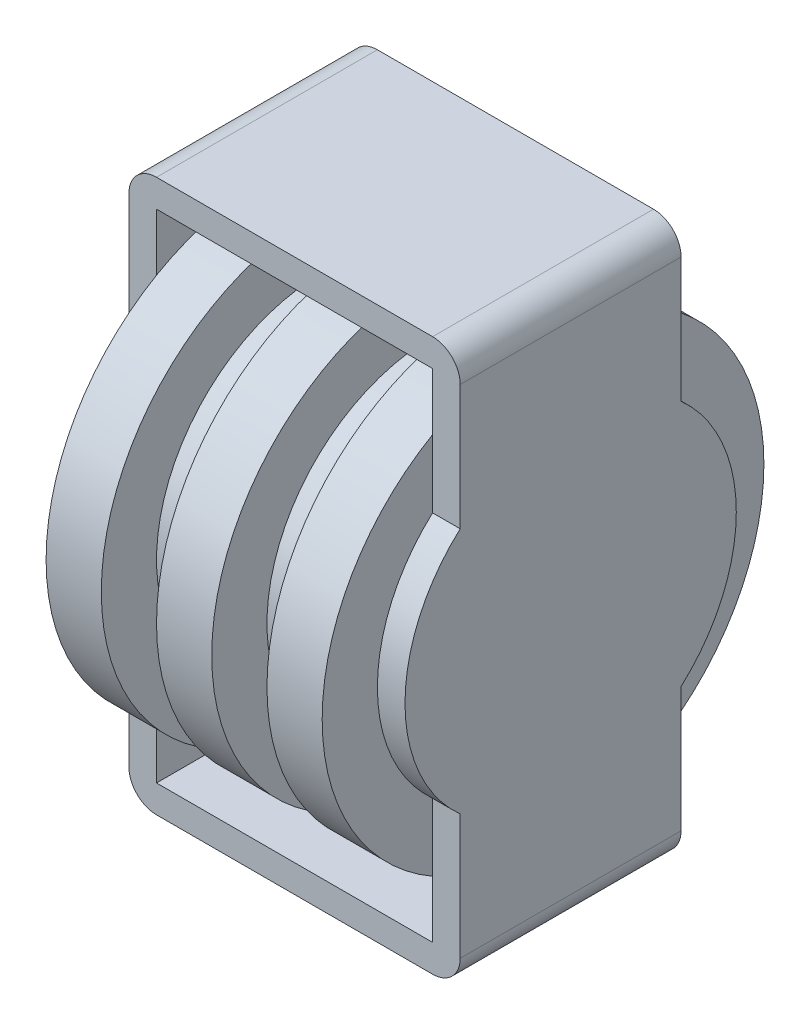
SolidWorks part; units mm, degrees
ref_plane "Front Plane" through (0, 0, 0) normal (0, 0, 1) x (1, 0, 0)
ref_plane "Top Plane" through (0, 0, 0) normal (0, 1, 0) x (1, 0, 0)
ref_plane "Right Plane" through (0, 0, 0) normal (1, 0, 0) x (0, 0, -1)
sketch "Sketch1" plane through (0, 0, 0) normal (1, 0, 0) x (0, 0, -1)
  line L0 (10, -22.5) -> (10, -25)
  line L2 (-10, -22.5) -> (-10, 22.5)
  line L3 (-10, 22.5) -> (10, 22.5)
  line L4 (10, -22.5) -> (10, 22.5)
  line L5 (-10, -22.5) -> (10, 22.5) construction
  line L6 (-10, 22.5) -> (10, -22.5) construction
  line L7 (10, -25) -> (-10, -25)
  line L8 (-10, -25) -> (-10, -22.5)
  circle A2 centre (0, 0) radius 15
  dimension "D1" = 2.5
  dimension "D4" = 30
  dimension "D2" = 20
  dimension "D3" = 45
extrude "Boss-Extrude1" add sketch "Sketch1" along normal blind 2.5
ref_plane "Plane2" through (2.5, 0, 0) normal (1, 0, 0) x (0, 0, -1)
sketch "Sketch2" plane through (2.5, 0, 0) normal (1, 0, 0) x (0, 0, -1)
  circle A0 centre (0, 0) radius 20
  dimension "D1" = 40
extrude "Boss-Extrude2" add sketch "Sketch2" along normal blind 5
ref_plane "Plane3" through (7.5, 0, 0) normal (1, 0, 0) x (0, 0, -1)
sketch "Sketch3" plane through (7.5, 0, 0) normal (1, 0, 0) x (0, 0, -1)
  circle A0 centre (0, 0) radius 15
  dimension "D1" = 30
extrude "Boss-Extrude3" add sketch "Sketch3" along normal blind 5
ref_plane "Plane4" through (12.5, 0, 0) normal (1, 0, 0) x (0, 0, -1)
sketch "Sketch4" plane through (12.5, 0, 0) normal (1, 0, 0) x (0, 0, -1)
  circle A0 centre (0, 0) radius 20
  dimension "D1" = 40
extrude "Boss-Extrude4" add sketch "Sketch4" along normal blind 5
ref_plane "Plane5" through (17.5, 0, 0) normal (1, 0, 0) x (0, 0, -1)
sketch "Sketch5" plane through (17.5, 0, 0) normal (1, 0, 0) x (0, 0, -1)
  circle A0 centre (0, 0) radius 15
  dimension "D1" = 30
extrude "Boss-Extrude5" add sketch "Sketch5" along normal blind 5
ref_plane "Plane6" through (22.5, 0, 0) normal (1, 0, 0) x (0, 0, -1)
sketch "Sketch6" plane through (22.5, 0, 0) normal (1, 0, 0) x (0, 0, -1)
  circle A0 centre (0, 0) radius 20
  dimension "D1" = 40
extrude "Boss-Extrude6" add sketch "Sketch6" along normal blind 5
ref_plane "Plane7" through (27.5, 0, 0) normal (1, 0, 0) x (0, 0, -1)
sketch "Sketch7" plane through (27.5, 0, 0) normal (1, 0, 0) x (0, 0, -1)
  line L0 (-10, -22.5) -> (-10, -25)
  line L2 (10, -22.5) -> (10, 22.5)
  line L3 (10, 22.5) -> (-10, 22.5)
  line L4 (-10, -22.5) -> (-10, 22.5)
  line L5 (10, -22.5) -> (-10, 22.5) construction
  line L6 (10, 22.5) -> (-10, -22.5) construction
  line L7 (-10, -25) -> (10, -25)
  line L8 (10, -25) -> (10, -22.5)
  point P0 (0, 0)
  dimension "D1" = 20
  dimension "D2" = 45
  dimension "D3" = 2.5
extrude "Boss-Extrude7" add sketch "Sketch7" along normal blind 2.5
ref_plane "Plane8" through (0, 22.5, 0) normal (0, 1, 0) x (1, 0, 0)
sketch "Sketch8" plane through (0, 22.5, 0) normal (0, 1, 0) x (1, 0, 0)
  line L1 (0, 10) -> (30, 10)
  line L2 (0, 10) -> (0, -10)
  line L3 (0, -10) -> (30, -10)
  line L4 (30, 10) -> (30, -10)
extrude "Boss-Extrude8" add sketch "Sketch8" along normal blind 2.5
ref_plane "Plane9" through (2.5, 0, 0) normal (1, 0, 0) x (0, 0, -1)
sketch "Sketch10" plane through (2.5, 0, 0) normal (1, 0, 0) x (0, 0, -1)
  line L0 (10, -17.3205) -> (10, -25) construction
  line L1 (-10, -25) -> (10, -25)
  line L2 (-10, -25) -> (-10, -22.5)
  line L3 (-10, -22.5) -> (10, -22.5)
  line L4 (10, -25) -> (10, -22.5)
  dimension "D1" = 2.5
extrude "Boss-Extrude9" add sketch "Sketch10" along normal blind 25
ref_plane "Plane10" through (30, 0, 0) normal (1, 0, 0) x (0, 0, -1)
sketch "Sketch11" plane through (30, 0, 0) normal (1, 0, 0) x (0, 0, -1)
  circle A0 centre (0, 0) radius 15
  dimension "D1" = 30
extrude "Boss-Extrude10" add sketch "Sketch11" against normal blind 2.5
ref_plane "Plane11" through (0, 0, 0) normal (-1, 0, 0) x (0, 0, 1)
sketch "Sketch12" plane through (0, 0, 0) normal (-1, 0, 0) x (0, 0, 1)
  circle A0 centre (0, 0) radius 15
  dimension "D1" = 30
extrude "Boss-Extrude11" add sketch "Sketch12" against normal blind 2.5
fillet "Fillet1" radius 2.5 2 edges at (30, 25, 0) (0, 25, 0)
fillet "Fillet2" radius 2.5 2 edges at (30, -25, 0) (0, -25, 0)
